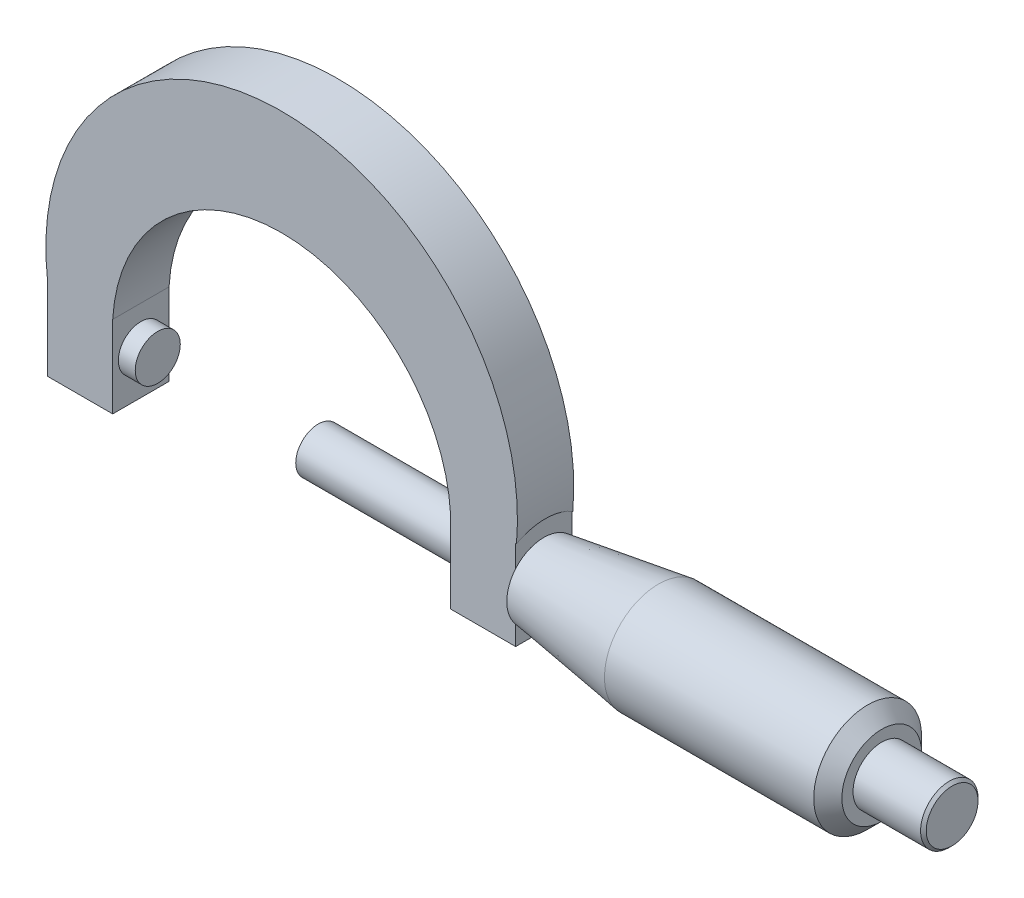
SolidWorks part; units mm, degrees
material "AISI 1020"
ref_plane "Front Plane" through (0, 0, 0) normal (0, 0, 1) x (1, 0, 0)
ref_plane "Top Plane" through (0, 0, 0) normal (0, 1, 0) x (1, 0, 0)
ref_plane "Right Plane" through (0, 0, 0) normal (1, 0, 0) x (0, 0, -1)
sketch "Sketch2" plane through (0, 0, 0) normal (0, 0, 1) x (1, 0, 0)
  line L0 (-872.8738, 0) -> (42770.8164, 0) construction
  line L1 (0, -872.8738) -> (0, 42770.8164) construction
  line L2 (-21.1105, -3.9166) -> (-15.24, -3.9166)
  line L3 (-21.1105, -3.9166) -> (-21.1105, 3.4702)
  line L5 (-15.24, -3.9166) -> (-15.24, 3.4702)
  line L10 (0, 17.8585) -> (0, 27.3553)
  arc A0 (-15.24, 3.4702) -> (0, 17.8585) centre (0, 2.5933) cw
  arc A1 (-21.1105, 3.4702) -> (0, 27.3553) centre (0, 6.0836) cw
  dimension "D1" = 15.24
extrude "Boss-Extrude1" add sketch "Sketch2" along normal mid plane 5.08
mirror "Mirror1" about plane through (0, 0, 0) normal (1, 0, 0) of "Boss-Extrude1"
sketch "Sketch3" plane through (21.1105, 0, 0) normal (1, 0, 0) x (0, 0, -1)
  circle A0 centre (0, 0) radius 4.8653
extrude "Boss-Extrude2" add sketch "Sketch3" along normal blind 30.48
sketch "Sketch4" plane through (0, 0, 0) normal (0, 0, 1) x (1, 0, 0)
  line L0 (21.1105, 3.3424) -> (21.1105, 4.8653)
  line L1 (51.5905, 4.8653) -> (21.2367, 4.8653) construction
  line L2 (31.4459, 4.8653) -> (21.1105, 3.3424)
  line L3 (21.1105, 4.1497) -> (21.1105, -4.8653) construction
  line L4 (21.1105, 4.8653) -> (31.4459, 4.8653)
revolve "Cut-Revolve1" cut sketch "Sketch4" angle 360 about axis through (51.5905, 0, 0) along (-1, 0, 0)
chamfer "Chamfer5" distance 1.27 angle 45 1 edges at (51.5905, 0, -4.8653)
sketch "Sketch5" plane through (51.5905, 0, 0) normal (1, 0, 0) x (0, 0, -1)
  circle A0 centre (0, 0) radius 2.5901
extrude "Boss-Extrude3" add sketch "Sketch5" along normal blind 6.35
chamfer "Chamfer6" distance 0.254 angle 45 1 edges at (57.9405, 0, -2.5901)
sketch "Sketch6" plane through (-15.24, 0, 0) normal (1, 0, 0) x (0, 0, -1)
  circle A0 centre (0, 0) radius 2.032
  dimension "D1" = 4.064
extrude "Boss-Extrude4" add sketch "Sketch6" along normal blind 1.524
sketch "Sketch7" plane through (15.24, 0, 0) normal (-1, 0, 0) x (0, 0, 1)
  circle A0 centre (0, 0) radius 2.032
  dimension "D1" = 4.064
extrude "Boss-Extrude5" add sketch "Sketch7" along normal blind 14.478
